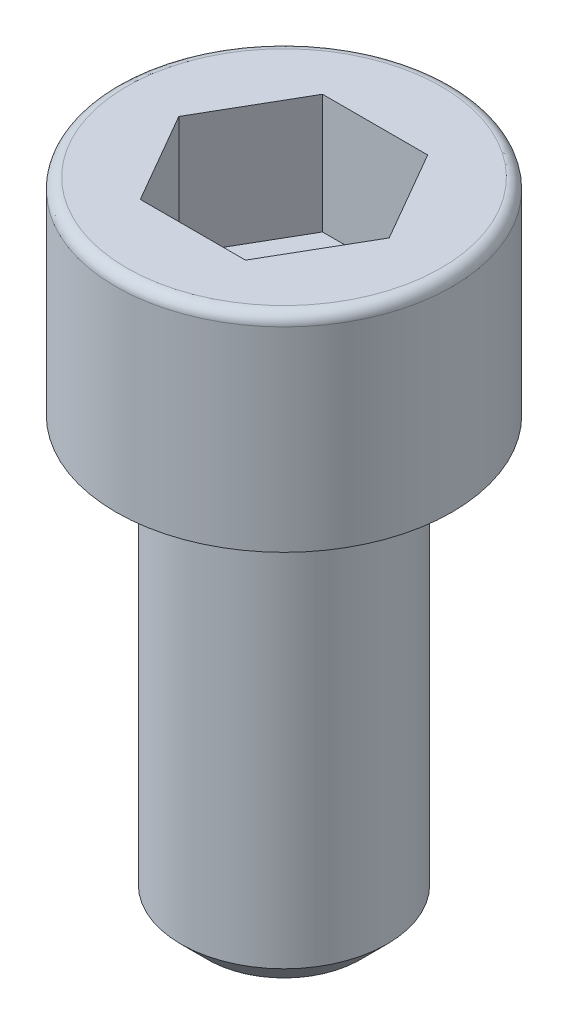
SolidWorks part; units mm, degrees
ref_plane "Front Plane" through (0, 0, 0) normal (0, 0, 1) x (1, 0, 0)
ref_plane "Top Plane" through (0, 0, 0) normal (0, 1, 0) x (1, 0, 0)
ref_plane "Right Plane" through (0, 0, 0) normal (1, 0, 0) x (0, 0, -1)
sketch "Sketch1" plane through (0, 0, 0) normal (0, 1, 0) x (1, 0, 0)
  circle A0 centre (0, 0) radius 3.875
extrude "Boss-Extrude1" add sketch "Sketch1" along normal blind 4.75
fillet "Fillet1" radius 0.25 1 edges at (0, 4.75, 3.875)
sketch "Sketch2" plane through (0, 4.75, 0) normal (0, 1, 0) x (1, 0, 0)
  line L0 (-1.8187, 1.05) -> (0, 0)
  line L1 (-2.4249, 0) -> (-1.2124, -2.1)
  line L2 (-1.2124, -2.1) -> (1.2124, -2.1)
  line L3 (1.2124, -2.1) -> (2.4249, 0)
  line L4 (2.4249, 0) -> (1.2124, 2.1)
  line L5 (1.2124, 2.1) -> (-1.2124, 2.1)
  line L6 (-1.2124, 2.1) -> (-2.4249, 0)
  circle A0 centre (0, 0) radius 2.1 construction
extrude "Cut-Extrude1" cut sketch "Sketch2" against normal blind 2.75
sketch "Sketch3" plane through (0, 0, 0) normal (0, -1, 0) x (1, 0, 0)
  circle A0 centre (0, 0) radius 2.375
extrude "Boss-Extrude2" add sketch "Sketch3" along normal blind 10
sketch "Sketch4" plane through (0, 0, 0) normal (1, 0, 0) x (0, 0, -1)
  line L0 (-2.375, -10) -> (-1.75, -10)
  line L1 (-2.375, -10) -> (2.375, -10) construction
  line L2 (-1.75, -10) -> (-2.375, -9.375)
  line L3 (-2.375, 0) -> (-2.375, -10) construction
  line L4 (0, -10) -> (0, 0)
  line L5 (-2.375, -10) -> (-2.375, -9.375)
revolve "Cut-Revolve1" cut sketch "Sketch4" angle 360 about L4
